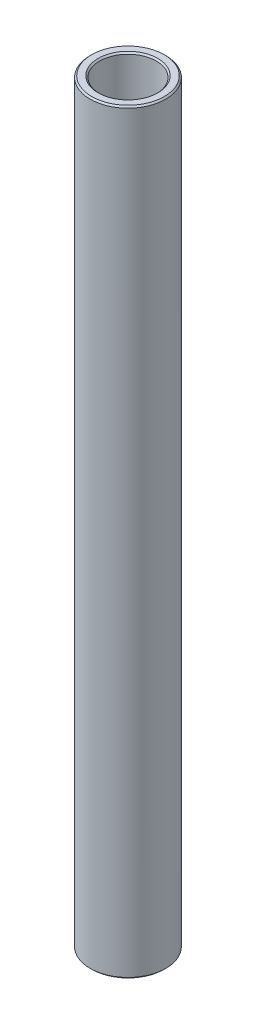
SolidWorks part; units mm, degrees
ref_plane "Front Plane" through (0, 0, 0) normal (0, 0, 1) x (1, 0, 0)
ref_plane "Top Plane" through (0, 0, 0) normal (0, 1, 0) x (1, 0, 0)
ref_plane "Right Plane" through (0, 0, 0) normal (1, 0, 0) x (0, 0, -1)
sketch "Sketch1" plane through (0, 0, 0) normal (0, 0, 1) x (1, 0, 0)
  line L0 (0, 11.6086) -> (0, -11.6086) construction
  line L1 (4.7625, 63.5) -> (6.35, 63.5)
  line L2 (6.35, 63.5) -> (6.35, -63.5)
  line L3 (6.35, -63.5) -> (4.7625, -63.5)
  line L4 (4.7625, -63.5) -> (4.7625, 63.5)
  line L5 (4.7625, 0) -> (0, 0) construction
  dimension "D1" = 9.525
  dimension "D2" = 12.7
  dimension "D3" = 127
revolve "Revolve1" add sketch "Sketch1" angle 360 about L0
chamfer "Chamfer1" distance 0.254 angle 45 4 edges at (-4.7625, -63.5, 0) (-6.35, -63.5, 0) (-6.35, 63.5, 0) (-4.7625, 63.5, 0)
